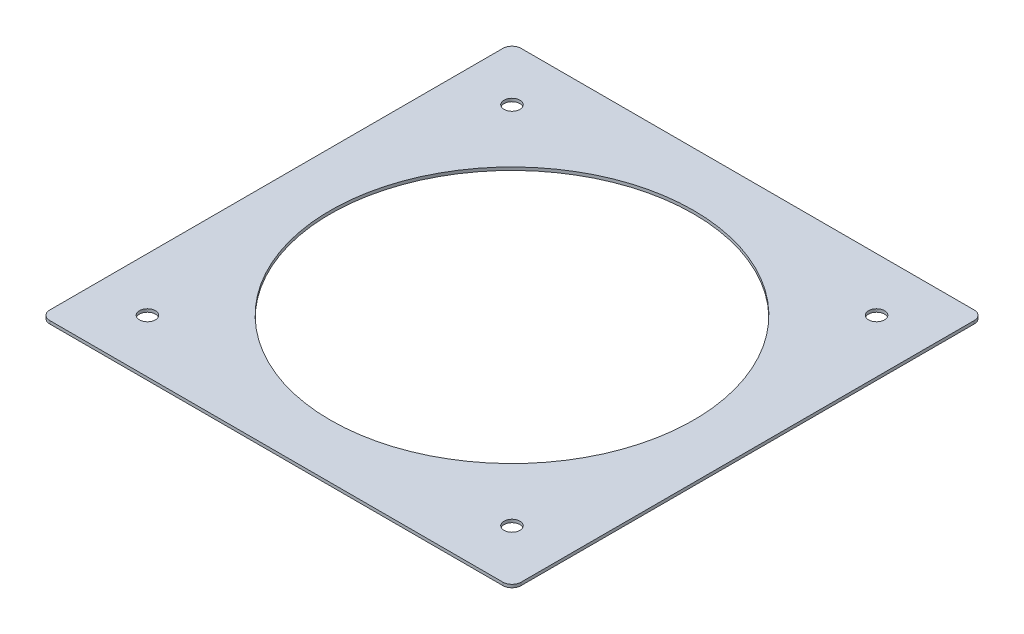
SolidWorks part; units mm, degrees
ref_plane "Front Plane" through (0, 0, 0) normal (0, 0, 1) x (1, 0, 0)
ref_plane "Top Plane" through (0, 0, 0) normal (0, 1, 0) x (1, 0, 0)
ref_plane "Right Plane" through (0, 0, 0) normal (1, 0, 0) x (0, 0, -1)
sketch "Sketch1" plane through (0, 0, 0) normal (0, 1, 0) x (1, 0, 0)
  line L0 (74.4455, 78.6361) -> (-75.2301, 78.6361)
  line L1 (-78.2437, 75.6225) -> (-78.2437, -74.0531)
  line L2 (-75.2301, -77.0667) -> (74.4455, -77.0667)
  line L3 (77.4591, -74.0531) -> (77.4591, 75.6225)
  line L4 (-78.2437, 78.6361) -> (-78.2437, 63.6361) construction
  line L5 (-78.2437, 78.6361) -> (-63.2437, 78.6361)
  line L6 (-63.2437, 78.6361) -> (-63.2437, 63.6361) construction
  line L7 (-63.2437, 63.6361) -> (-78.2437, 63.6361) construction
  line L8 (-63.2437, 60.9984) -> (-63.2437, 63.6361) construction
  line L9 (-63.2437, 63.6361) -> (-60.6061, 63.6361) construction
  line L10 (-0.3923, -77.0667) -> (-0.3923, 78.6361) construction
  line L11 (77.4591, 0.7847) -> (-78.2437, 0.7847) construction
  arc A0 (-75.2301, 78.6361) -> (-78.2437, 75.6225) centre (-75.2301, 75.6225) ccw
  arc A1 (-78.2437, -74.0531) -> (-75.2301, -77.0667) centre (-75.2301, -74.0531) ccw
  arc A2 (74.4455, -77.0667) -> (77.4591, -74.0531) centre (74.4455, -74.0531) ccw
  arc A3 (77.4591, 75.6225) -> (74.4455, 78.6361) centre (74.4455, 75.6225) ccw
  circle A4 centre (-60.6061, 60.9984) radius 2.6376
  circle A5 centre (-60.6061, -59.4291) radius 2.6376
  circle A6 centre (59.8214, -59.4291) radius 2.6376
  circle A7 centre (59.8214, 60.9984) radius 2.6376
  circle A8 centre (-0.3923, 0.7847) radius 60
  dimension "D3" = 120
  dimension "D1" = 15
  dimension "D2" = 15
extrude "Boss-Extrude1" add sketch "Sketch1" along normal blind 1 contours L3 A3 L0 A0 L1 A1 L2 A2 A8 A5 A4 A6 A7
